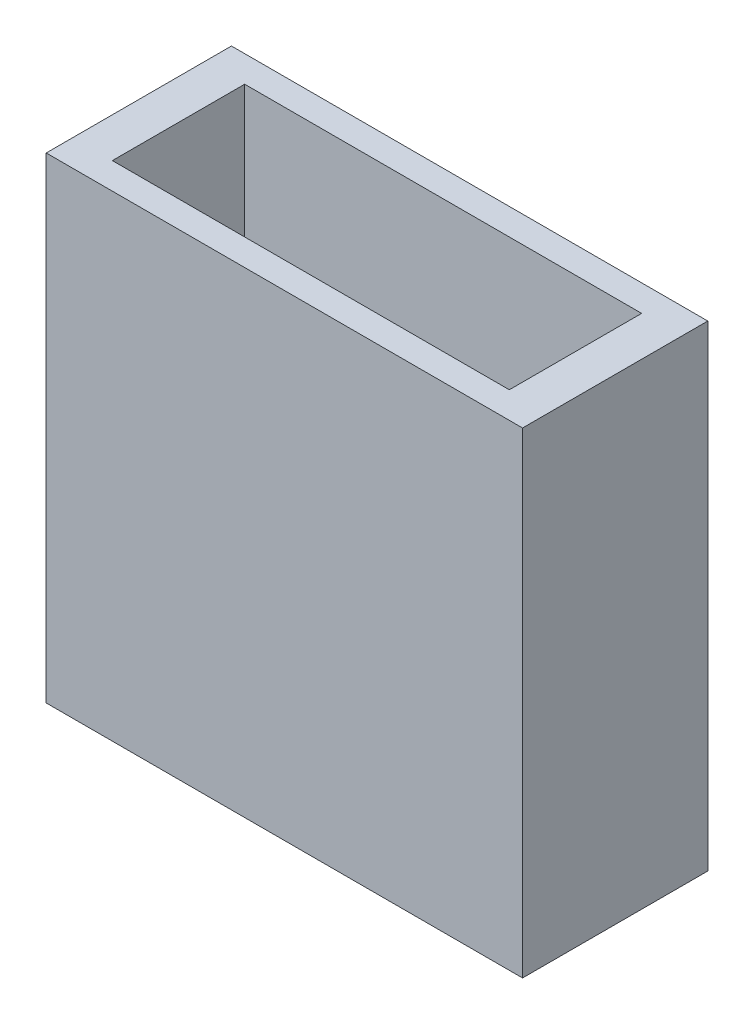
SolidWorks part; units mm, degrees
ref_plane "Front Plane" through (0, 0, 0) normal (0, 0, 1) x (1, 0, 0)
ref_plane "Top Plane" through (0, 0, 0) normal (0, 1, 0) x (1, 0, 0)
ref_plane "Right Plane" through (0, 0, 0) normal (1, 0, 0) x (0, 0, -1)
sketch "Sketch1" plane through (0, 0, 0) normal (0, 1, 0) x (1, 0, 0)
  line L1 (0, 0) -> (45.72, 0)
  line L2 (0, 0) -> (0, 17.78)
  line L3 (0, 17.78) -> (45.72, 17.78)
  line L4 (45.72, 0) -> (45.72, 17.78)
  dimension "D1" = 45.72
  dimension "D2" = 17.78
extrude "Boss-Extrude1" add sketch "Sketch1" along normal blind 45.72
ref_plane "Plane1" through (0, 45.72, 0) normal (0, 1, 0) x (1, 0, 0)
sketch "Sketch2" plane through (0, 45.72, 0) normal (0, 1, 0) x (1, 0, 0)
  line L0 (0, 17.78) -> (0, 0) construction
  line L1 (3.81, 2.54) -> (41.91, 2.54)
  line L2 (3.81, 2.54) -> (3.81, 15.24)
  line L3 (3.81, 15.24) -> (41.91, 15.24)
  line L4 (41.91, 2.54) -> (41.91, 15.24)
  line L5 (45.72, 0) -> (45.72, 17.78) construction
  line L6 (0, 0) -> (45.72, 0) construction
  line L7 (45.72, 17.78) -> (0, 17.78) construction
  dimension "D1" = 3.81
  dimension "D2" = 3.81
  dimension "D3" = 2.54
  dimension "D4" = 2.54
extrude "Cut-Extrude1" cut sketch "Sketch2" against normal blind 41.91
sketch "Sketch4" plane through (0, 0, 0) normal (0, 0, 1) x (1, 0, 0)
  line L0 (0, 0) -> (25.4, 4.7076)
  line L1 (0, 0) -> (45.72, 0) construction
  point P5 (29.6035, 5.4867)
  dimension "D1" = 10.5
  dimension "D2" = 25.4
sketch "Sketch5" plane through (0, 0, 0) normal (0, 1, 0) x (1, 0, 0)
  line L0 (0, 0) -> (3.9734, 25.0873)
  line L1 (0, 0) -> (25.4, 0) construction
  point P5 (0, 0)
  point P6 (0, 0)
  point P7 (0, 0)
  dimension "D1" = 81
  dimension "D2" = 25.4
ref_plane "Plane3" through (0, 0, 0) normal (0.1822, -0.9828, 0.0289) x (0.9745, 0.1765, -0.1385)
sketch "Sketch6" plane through (0, 0, 0) normal (0.1822, -0.9828, 0.0289) x (0.9745, 0.1765, -0.1385)
  line L0 (44.5542, 5.9899) -> (47.0164, -11.6113) construction
  line L1 (47.0164, -11.6113) -> (2.4622, -17.6012) construction
  circle A0 centre (23.1283, -5.8529) radius 3.048
  circle A1 centre (16.0797, -6.8005) radius 3.048
  circle A2 centre (30.1769, -4.9052) radius 3.048
  dimension "D2" = 6.096
  dimension "D4" = 6.096
  dimension "D5" = 6.096
  dimension "D1" = 22.86
  dimension "D3" = 8.89
  dimension "D6" = 7.112
  dimension "D7" = 7.112
  dimension "D8" = 8.89
  dimension "D9" = 8.89
extrude "Cut-Extrude2" cut sketch "Sketch6" against normal blind 15.24 and the other way through all
equation "\"x\"=0.296138"
